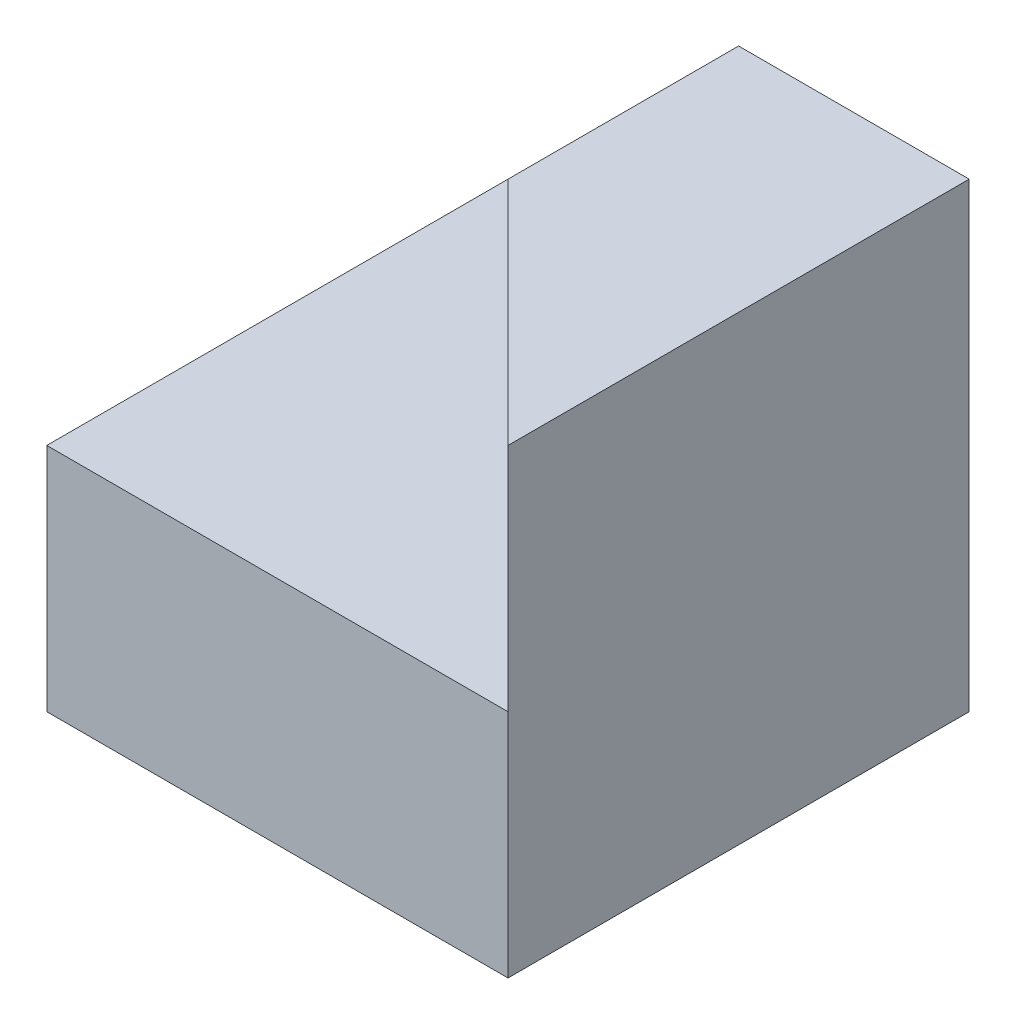
SolidWorks part; units mm, degrees
ref_plane "Front Plane" through (0, 0, 0) normal (0, 0, 1) x (1, 0, 0)
ref_plane "Top Plane" through (0, 0, 0) normal (0, 1, 0) x (1, 0, 0)
ref_plane "Right Plane" through (0, 0, 0) normal (1, 0, 0) x (0, 0, -1)
sketch "Sketch1" plane through (0, 0, 0) normal (0, 0, 1) x (1, 0, 0)
  line L1 (0, 0) -> (40, 0)
  line L2 (0, 0) -> (0, 20)
  line L3 (0, 20) -> (40, 20)
  line L4 (40, 0) -> (40, 20)
  dimension "D1" = 40
  dimension "D2" = 20
extrude "Boss-Extrude1" add sketch "Sketch1" along normal blind 40
sketch "Sketch2" plane through (0, 0, 40) normal (0, 0, 1) x (1, 0, 0)
  line L1 (40, 20) -> (20, 20)
  line L2 (40, 20) -> (40, 40)
  line L3 (40, 40) -> (20, 40)
  line L4 (20, 20) -> (20, 40)
  dimension "D1" = 20
  dimension "D2" = 20
extrude "Boss-Extrude2" add sketch "Sketch2" against normal blind 40
sketch "Sketch3" plane through (0, 40, 0) normal (0, 1, 0) x (1, 0, 0)
  line L0 (40, -20) -> (20, 0)
  line L1 (40, 0) -> (40, -40) construction
  line L2 (20, 0) -> (20, -40)
  line L3 (20, -40) -> (40, -20)
  line L4 (20, -40) -> (40, -40)
  line L5 (40, -40) -> (40, 0)
  line L6 (40, 0) -> (20, 0)
  line M1 (20, -40) -> (40, -40)
  line M2 (40, -40) -> (40, 0)
extrude "Cut-Extrude2" cut sketch "Sketch3" against normal blind 20 contours L3 M1 M2
sketch "Sketch4" plane through (0, 40, 0) normal (0, 1, 0) x (1, 0, 0)
  line L0 (40, 0) -> (20, -20)
  line L1 (20, 0) -> (20, -40) construction
  line L2 (20, -20) -> (20, 0)
  line L3 (20, 0) -> (40, 0)
extrude "Cut-Extrude3" cut sketch "Sketch4" against normal blind 20
sketch "Sketch5" plane through (0, 20, 0) normal (0, 1, 0) x (1, 0, 0)
  line L0 (20, -20) -> (20, 0)
  line L1 (40, 0) -> (0, 0) construction
  line L2 (20, 0) -> (40, 0)
  line L3 (40, 0) -> (20, -20)
  line L4 (20, -20) -> (20.0602, -19.9601)
  line M2 (20, -20) -> (40, 0)
  line M3 (40, 0) -> (0, 0)
extrude "Boss-Extrude3" add sketch "Sketch5" along normal blind 20 contours L0 M2 M3
sketch "Sketch6" plane through (0, 20, 0) normal (0, 1, 0) x (1, 0, 0)
  line L0 (20, -40) -> (40, -40)
  line L1 (40, -40) -> (40, -20)
  line L2 (40, -20) -> (20, -40)
extrude "Boss-Extrude4" add sketch "Sketch6" along normal blind 20
sketch "Sketch7" plane through (0, 40, 0) normal (0, 1, 0) x (1, 0, 0)
  line L0 (20, -40) -> (40, -20)
  line L1 (40, 0) -> (40, -40) construction
  line L2 (40, -20) -> (20, -20)
  line L3 (20, 0) -> (20, -40) construction
  line L4 (20, -20) -> (20, -40)
  line L5 (20, -40) -> (20, -20)
  line L6 (20, -20) -> (40, -40)
  line L7 (40, -40) -> (20, -40)
  line M3 (20, 0) -> (20, -40)
  line M4 (20, -40) -> (40, -40)
extrude "Cut-Extrude4" cut sketch "Sketch7" against normal blind 20 contours L6 L0 M3 | L6 L0 M4
